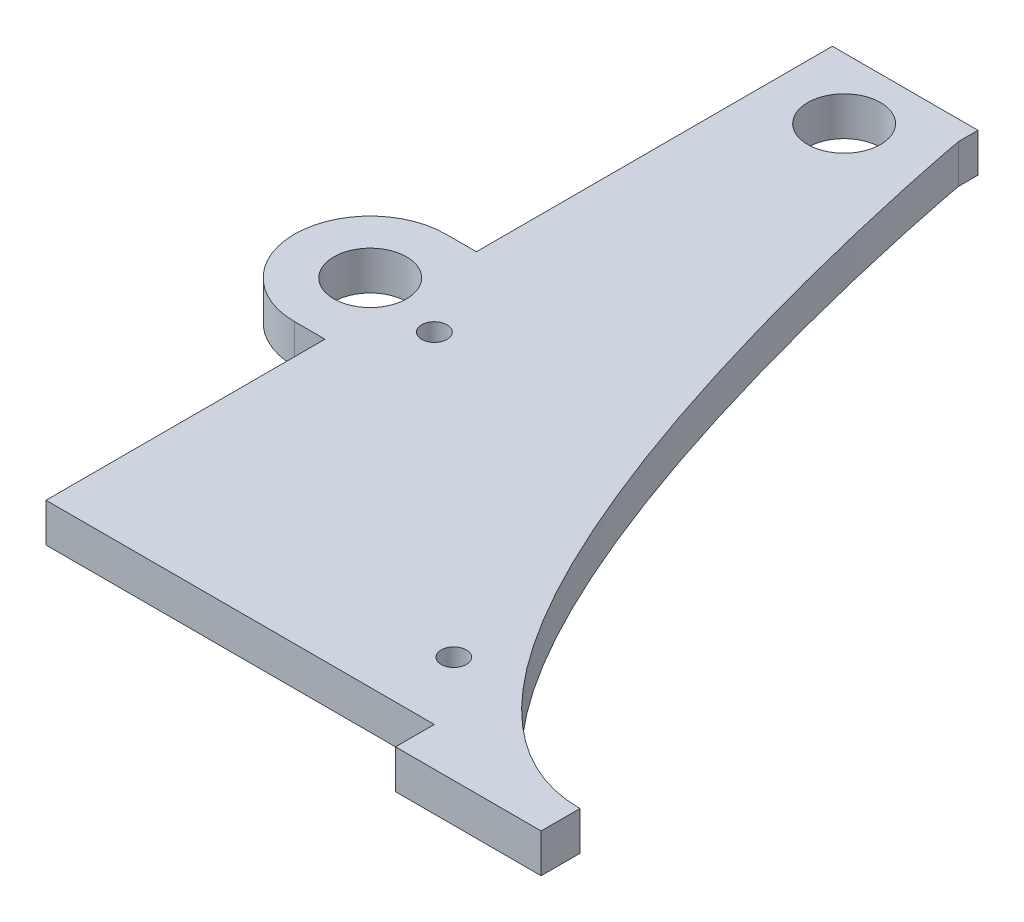
SolidWorks part; units mm, degrees
ref_plane "Front Plane" through (0, 0, 0) normal (0, 0, 1) x (1, 0, 0)
ref_plane "Top Plane" through (0, 0, 0) normal (0, 1, 0) x (1, 0, 0)
ref_plane "Right Plane" through (0, 0, 0) normal (1, 0, 0) x (0, 0, -1)
sketch "Sketch1" plane through (0, 0, 0) normal (0, 1, 0) x (1, 0, 0)
  line L0 (9.525, -53.975) -> (60.325, -53.975) construction
  line L1 (-9.525, -53.975) -> (9.525, -53.975) construction
  line L2 (-9.525, -53.975) -> (-9.525, 53.975) construction
  line L3 (-9.525, 53.975) -> (9.525, 53.975)
  line L4 (9.525, -53.975) -> (9.525, 53.975) construction
  line L5 (-9.525, -53.975) -> (9.525, 53.975) construction
  line L6 (-9.525, 53.975) -> (9.525, -53.975) construction
  line L7 (0, 53.975) -> (0, 45.9867) construction
  line L8 (-9.525, 50.7492) -> (9.525, 50.7492) construction
  line L9 (9.525, 51.435) -> (9.525, 53.975)
  line L10 (60.325, -53.975) -> (60.325, -48.895) construction
  line L11 (60.325, -48.895) -> (-9.525, -48.895) construction
  line L12 (60.325, -53.975) -> (60.325, -48.895) construction
  line L13 (60.325, -48.895) -> (-9.525, -48.895)
  line L14 (-9.525, -48.895) -> (-9.525, 53.975)
  line L15 (31.115, -19.685) -> (31.115, -48.895) construction
  circle A0 centre (0, 45.9867) radius 4.7625
  spline S0 degree 3 poles (9.525, 51.435) (9.525, 51.2145) (27.8191, -48.895) (60.325, -48.895) knots 0 0 0 0 1 1 1 1
  point P4 (0, 0)
  dimension "D5" = 9.525
  dimension "D1" = 107.95
  dimension "D2" = 19.05
  dimension "D3" = 50.8
  dimension "D4" = 2.54
  dimension "D6" = 104.7242
  dimension "D7" = 5.08
  dimension "D8" = 40.64
  dimension "D9" = 29.21
extrude "Boss-Extrude1" add sketch "Sketch1" along normal blind 5.08
sketch "Sketch4" plane through (0, 5.08, 0) normal (0, 1, 0) x (1, 0, 0)
  line L0 (-9.525, 53.975) -> (-9.525, -48.895) construction
  line L1 (60.325, -48.895) -> (41.275, -48.895)
  line L2 (60.325, -48.895) -> (60.325, -53.975)
  line L3 (60.325, -53.975) -> (41.275, -53.975)
  line L4 (41.275, -48.895) -> (41.275, -53.975)
  line L5 (60.325, -48.895) -> (41.275, -53.975) construction
  line L6 (60.325, -53.975) -> (41.275, -48.895) construction
  point P4 (50.8, -51.435)
  dimension "D1" = 50.8
  dimension "D2" = 5.08
extrude "Boss-Extrude2" add sketch "Sketch4" against normal up to surface (5.08 mm away) up to face at (17.145, 0, -2.286)
sketch "Sketch6" plane through (0, 0, 0) normal (0, -1, 0) x (1, 0, 0)
  line L0 (-9.525, 2.4976) -> (-13.5128, 2.4976) construction
  line L1 (-9.525, -53.975) -> (-9.525, 48.895) construction
  line L2 (-13.5128, 12.4036) -> (-9.525, 12.4036)
  line L3 (-13.5128, -7.4084) -> (-9.525, -7.4084)
  line L4 (-9.525, 12.4036) -> (-9.525, 11.5655)
  line L5 (-9.525, -7.4084) -> (-9.525, -6.5703)
  line L7 (41.275, 53.975) -> (60.325, 53.975) construction
  circle A0 centre (-13.5128, 2.4976) radius 4.7625
  arc A1 (-9.525, -6.5703) -> (-9.525, 11.5655) centre (-13.5128, 2.4976) ccw
  arc A2 (-13.5128, 12.4036) -> (-13.5128, -7.4084) centre (-13.5128, 2.4976) ccw
  dimension "D1" = 9.525
  dimension "D3" = 9.906
  dimension "D2" = 3.9878
  dimension "D4" = 51.4774
extrude "Boss-Extrude3" add sketch "Sketch6" against normal blind 5.08
sketch "Sketch8" plane through (0, 5.08, 0) normal (0, 1, 0) x (1, 0, 0)
  circle A0 centre (-13.5128, -2.4976) radius 4.7625
extrude "Cut-Extrude2" cut sketch "Sketch8" against normal through all
sketch "Sketch5" plane through (0, 0, 0) normal (0, -1, 0) x (1, 0, 0)
  circle A1 centre (34.925, 40.005) radius 1.651
  circle A3 centre (-3.175, 4.445) radius 1.6607
extrude "Cut-Extrude1" cut sketch "Sketch5" against normal through all both
